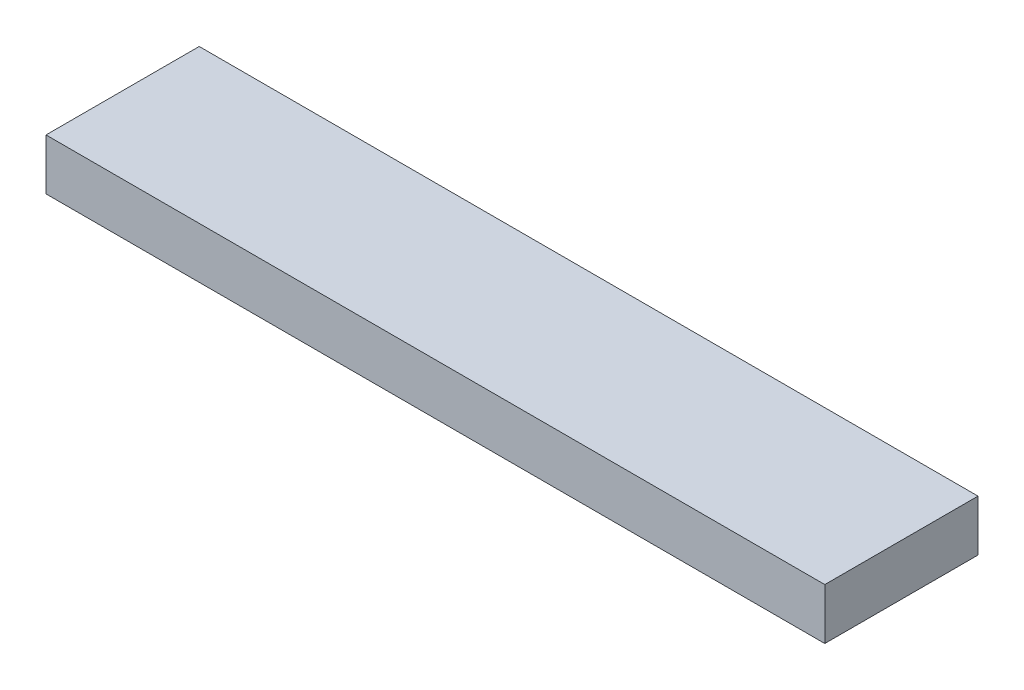
SolidWorks part; units mm, degrees
material "Plain Carbon Steel"
ref_plane "Front Plane" through (0, 0, 0) normal (0, 0, 1) x (1, 0, 0)
ref_plane "Top Plane" through (0, 0, 0) normal (0, 1, 0) x (1, 0, 0)
ref_plane "Right Plane" through (0, 0, 0) normal (1, 0, 0) x (0, 0, -1)
sketch "Sketch1" plane through (0, 0, 0) normal (0, 1, 0) x (1, 0, 0)
  line L1 (-96.8375, 19.05) -> (96.8375, 19.05)
  line L2 (-96.8375, 19.05) -> (-96.8375, -19.05)
  line L3 (-96.8375, -19.05) -> (96.8375, -19.05)
  line L4 (96.8375, 19.05) -> (96.8375, -19.05)
  line L5 (-96.8375, 19.05) -> (96.8375, -19.05) construction
  line L6 (-96.8375, -19.05) -> (96.8375, 19.05) construction
  point P0 (0, 0)
  dimension "D1" = 193.675
  dimension "D2" = 38.1
extrude "Boss-Extrude1" add sketch "Sketch1" along normal mid plane 12.7
sketch "Sketch2" plane through (0, 0, -19.05) normal (0, 0, -1) x (-1, 0, 0)
  line L0 (-96.8375, 0) -> (96.8375, 0) construction
  line L1 (-96.8375, 6.35) -> (-96.8375, -6.35) construction
  line L2 (96.8375, 6.35) -> (96.8375, -6.35) construction
  line L3 (0, 6.35) -> (0, -6.35) construction
  line L4 (-96.8375, 6.35) -> (96.8375, 6.35) construction
  line L5 (-96.8375, -6.35) -> (96.8375, -6.35) construction
